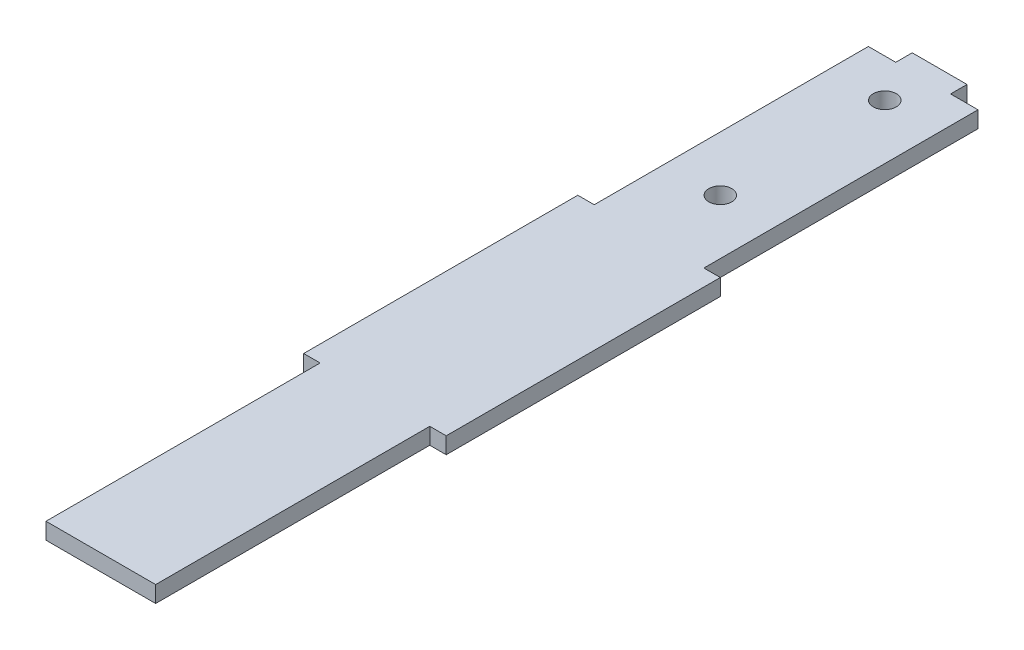
SolidWorks part; units mm, degrees
ref_plane "Front Plane" through (0, 0, 0) normal (0, 0, 1) x (1, 0, 0)
ref_plane "Top Plane" through (0, 0, 0) normal (0, 1, 0) x (1, 0, 0)
ref_plane "Right Plane" through (0, 0, 0) normal (1, 0, 0) x (0, 0, -1)
sketch "Sketch1" plane through (0, 0, 0) normal (0, 1, 0) x (1, 0, 0)
  line L0 (15, 0) -> (20, 0)
  line L1 (0, 0) -> (5, 0)
  line L2 (0, 0) -> (0, -50)
  line L3 (0, -150) -> (20, -150)
  line L4 (20, 0) -> (20, -50)
  line L5 (0, -50) -> (-3, -50)
  line L7 (0, -100) -> (-3, -100)
  line L8 (-3, -50) -> (-3, -100)
  line L9 (20, -50) -> (23, -50)
  line L11 (20, -100) -> (23, -100)
  line L12 (23, -50) -> (23, -100)
  line L13 (5, 3) -> (15, 3)
  line L14 (5, 3) -> (5, 0)
  line L16 (15, 3) -> (15, 0)
  line L17 (0, -100) -> (0, -150)
  line L18 (20, -100) -> (20, -150)
  dimension "D1" = 20
  dimension "D2" = 150
  dimension "D3" = 3
  dimension "D4" = 10
  dimension "D5" = 50
extrude "Boss-Extrude1" add sketch "Sketch1" along normal blind 3
sketch "Sketch2" plane through (0, 3, 0) normal (0, 1, 0) x (1, 0, 0)
  line L0 (10, 3) -> (10, -150) construction
  line L1 (15, 3) -> (5, 3) construction
  line L2 (0, -150) -> (20, -150) construction
  line L3 (20, 0) -> (15, 0) construction
  circle A0 centre (10, -7) radius 2.1
  circle A1 centre (10, -37) radius 2.1
  dimension "D1" = 4.2
  dimension "D2" = 7
  dimension "D3" = 30
extrude "Cut-Extrude1" cut sketch "Sketch2" against normal through all
